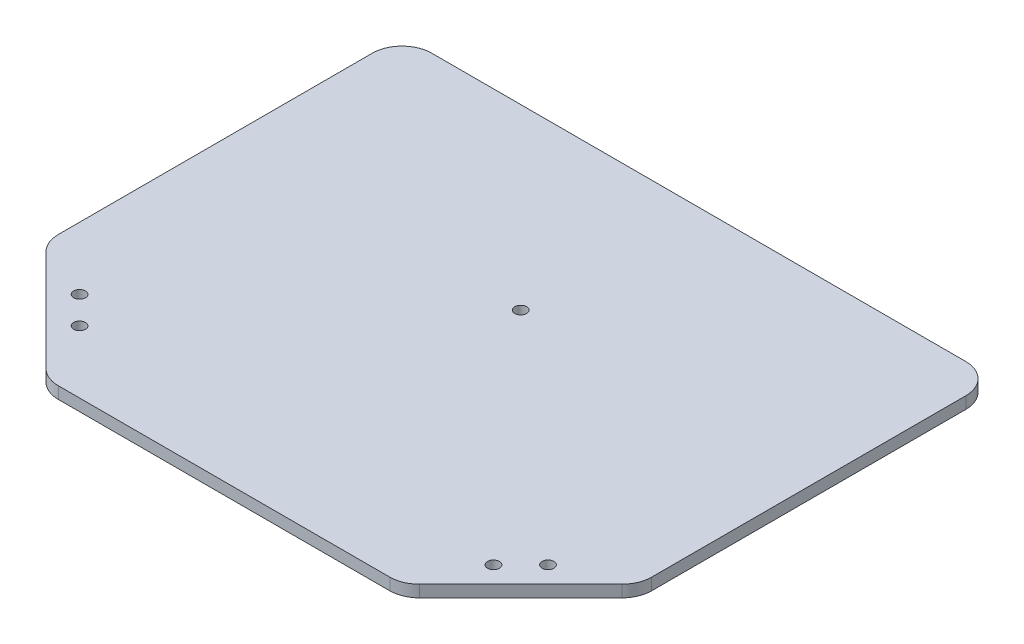
SolidWorks part; units mm, degrees
ref_plane "前视基准面" through (0, 0, 0) normal (0, 0, 1) x (1, 0, 0)
ref_plane "上视基准面" through (0, 0, 0) normal (0, 1, 0) x (1, 0, 0)
ref_plane "右视基准面" through (0, 0, 0) normal (1, 0, 0) x (0, 0, -1)
other "Configuration Table"
sketch "草图1" plane through (0, 0, 0) normal (0, 1, 0) x (1, 0, 0)
  line L0 (-227.5051, 0) -> (214.8307, 0) construction
  line L1 (0, -181.0695) -> (0, 185.6337) construction
  line L4 (-100, 60) -> (-100, -60)
  line L14 (60, -100) -> (-60, -100)
  line L15 (-60, -100) -> (-100, -60)
  line L16 (100, 60) -> (100, -60)
  line L17 (100, -60) -> (60, -100)
  line L18 (-100, 60) -> (100, 60)
  point P15 (0, -100)
  point P24 (-75, 0)
  dimension "D1" = 100
  dimension "D2" = 100
  dimension "D3" = 120
  dimension "D4" = 60
extrude "凸台-拉伸1" add sketch "草图1" along normal blind 4
sketch "草图2" plane through (0, 4, 0) normal (0, 1, 0) x (1, 0, 0)
  line L0 (-100, 0) -> (100, 0) construction
  line L1 (-100, 60) -> (-100, -60) construction
  line L2 (100, -60) -> (100, 60) construction
  line L3 (0, 60) -> (0, -100) construction
  line L4 (100, 60) -> (-100, 60) construction
  line L5 (-60, -100) -> (60, -100) construction
  circle A0 centre (0, 0) radius 2
extrude "切除-拉伸1" cut sketch "草图2" against normal through all
fillet "圆角1" radius 10 6 edges at (-60, 2, 100) (-100, 2, 60) (-100, 2, -60) (100, 2, -60) (100, 2, 60) (60, 2, 100)
sketch "草图4" plane through (0, 0, 0) normal (0, 1, 0) x (1, 0, 0)
  line L0 (0, 0) -> (-80, -80) construction
  line L1 (-97.0711, -62.9289) -> (-62.9289, -97.0711) construction
  line L2 (0, 60) -> (0, -100) construction
  line L3 (90, 60) -> (-90, 60) construction
  line L4 (-55.8579, -100) -> (55.8579, -100) construction
  line L5 (-100, 0) -> (100, 0) construction
  line L6 (-100, 50) -> (-100, -55.8579) construction
  line L7 (100, -55.8579) -> (100, 50) construction
  line L8 (-78.9393, -69.747) -> (-69.747, -78.9393) construction
  circle A0 centre (-78.9393, -69.747) radius 2
  circle A1 centre (-69.747, -78.9393) radius 2
  circle A2 centre (69.747, -78.9393) radius 2
  circle A3 centre (78.9393, -69.747) radius 2
  point P19 (-74.3431, -74.3431)
  dimension "D3" = 4
  dimension "D4" = 4
  dimension "D1" = 13
  dimension "D2" = 8
extrude "切除-拉伸2" cut sketch "草图4" along normal through all
